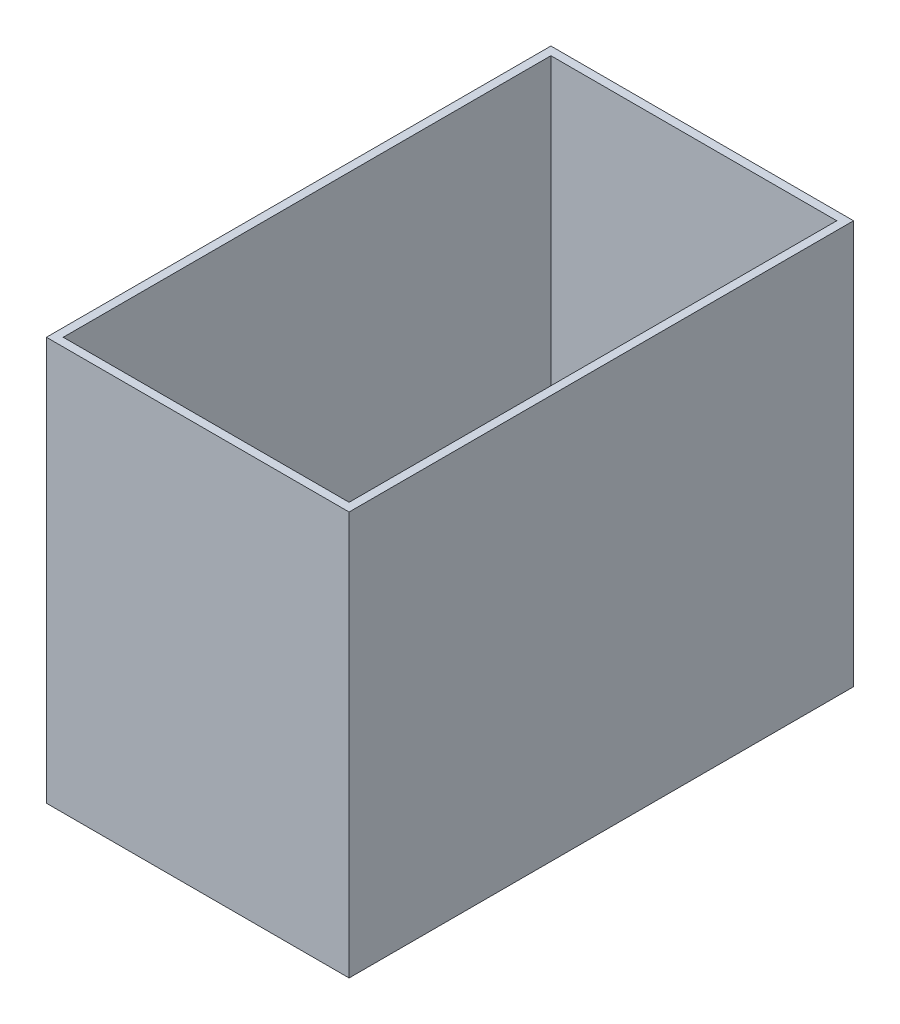
SolidWorks part; units mm, degrees
ref_plane "Front Plane" through (0, 0, 0) normal (0, 0, 1) x (1, 0, 0)
ref_plane "Top Plane" through (0, 0, 0) normal (0, 1, 0) x (1, 0, 0)
ref_plane "Right Plane" through (0, 0, 0) normal (1, 0, 0) x (0, 0, -1)
sketch "Sketch1" plane through (0, 0, 0) normal (0, 1, 0) x (1, 0, 0)
  line L1 (0, 0) -> (228.6, 0)
  line L2 (0, 0) -> (0, 381)
  line L3 (0, 381) -> (228.6, 381)
  line L4 (228.6, 0) -> (228.6, 381)
  dimension "D1" = 228.6
  dimension "D2" = 381
extrude "Boss-Extrude1" add sketch "Sketch1" along normal blind 304.8
sketch "Sketch2" plane through (0, 304.8, 0) normal (0, 1, 0) x (1, 0, 0)
  line L0 (228.6, 381) -> (0, 381) construction
  line L1 (6.35, 374.65) -> (222.25, 374.65)
  line L2 (6.35, 374.65) -> (6.35, 6.35)
  line L3 (6.35, 6.35) -> (222.25, 6.35)
  line L4 (222.25, 374.65) -> (222.25, 6.35)
  line L5 (0, 0) -> (228.6, 0) construction
  line L6 (228.6, 0) -> (228.6, 381) construction
  line L7 (0, 381) -> (0, 0) construction
  dimension "D1" = 6.35
  dimension "D2" = 6.35
  dimension "D3" = 6.35
  dimension "D4" = 6.35
extrude "Cut-Extrude1" cut sketch "Sketch2" against normal blind 298.45
